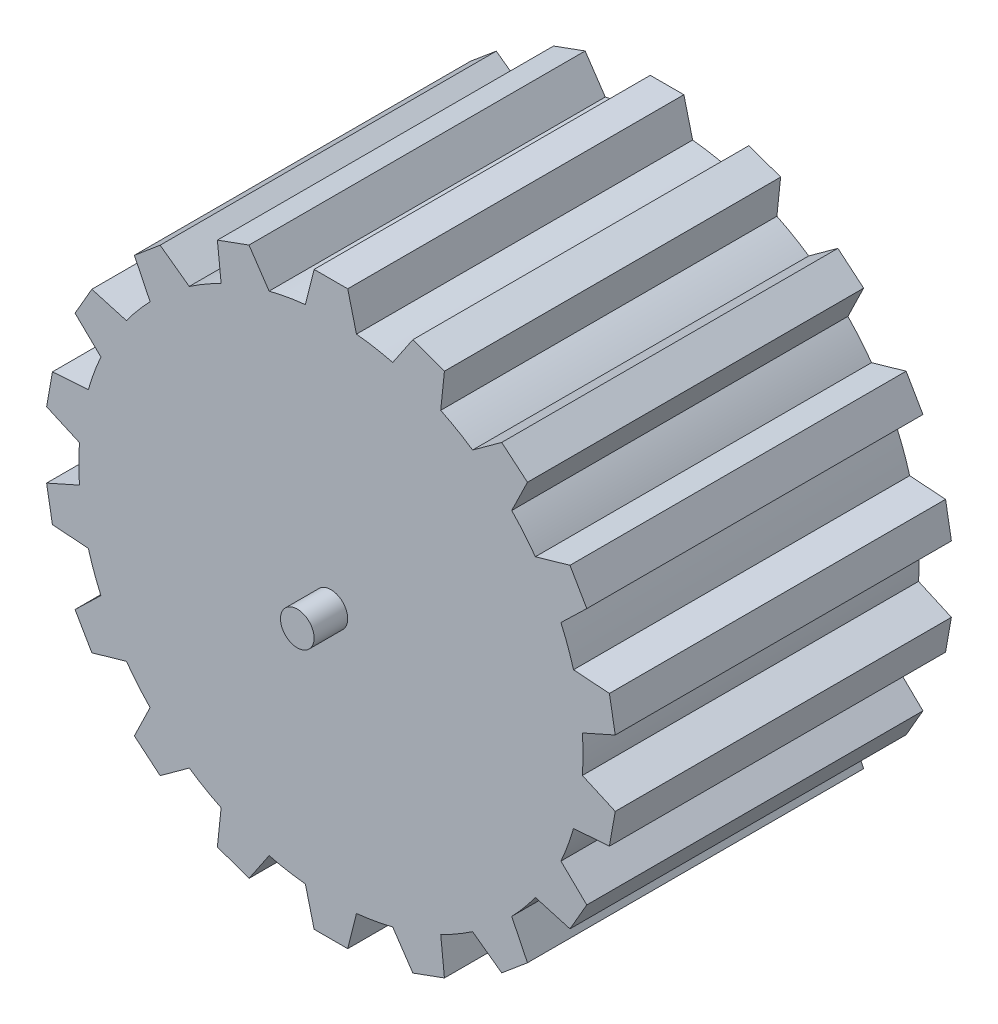
SolidWorks part; units mm, degrees
ref_plane "Front Plane" through (0, 0, 0) normal (0, 0, 1) x (1, 0, 0)
ref_plane "Top Plane" through (0, 0, 0) normal (0, 1, 0) x (1, 0, 0)
ref_plane "Right Plane" through (0, 0, 0) normal (1, 0, 0) x (0, 0, -1)
sketch "Sketch1" plane through (0, 0, 0) normal (0, 0, 1) x (1, 0, 0)
  circle A0 centre (0, 0) radius 15
  dimension "D1" = 30
extrude "Boss-Extrude1" add sketch "Sketch1" along normal blind 20
sketch "Sketch2" plane through (0, 0, 20) normal (0, 0, 1) x (1, 0, 0)
  line L0 (0, 15) -> (0, 17) construction
  line L1 (0, 17) -> (0, 15) construction
  line L2 (0, 15) -> (0, 13) construction
  line L3 (0, 17) -> (1, 17)
  line L4 (0, 17) -> (-1, 17)
  line L5 (0, 13) -> (2, 13)
  line L6 (0, 13) -> (-2, 13)
  line L7 (2, 13) -> (1, 17)
  line L8 (-1, 17) -> (-2, 13)
  circle A0 centre (0, 0) radius 15 construction
  dimension "D1" = 2
  dimension "D2" = 2
  dimension "D3" = 1
  dimension "D4" = 1
  dimension "D5" = 2
  dimension "D6" = 2
extrude "Boss-Extrude2" add sketch "Sketch2" against normal blind 20
pattern_circular "CirPattern1" count 18 every 20 about axis through (0, 0, 0) along (0, 0, 1) of "Boss-Extrude2"
sketch "Sketch3" plane through (0, 0, 0) normal (0, 0, -1) x (-1, 0, 0)
  circle A0 centre (0, 0) radius 1
  dimension "D1" = 2
extrude "Boss-Extrude3" add sketch "Sketch3" along normal blind 2
sketch "Sketch4" plane through (0, 0, 20) normal (0, 0, 1) x (1, 0, 0)
  circle A0 centre (0, 0) radius 1
  dimension "D1" = 2
extrude "Boss-Extrude4" add sketch "Sketch4" along normal blind 2
